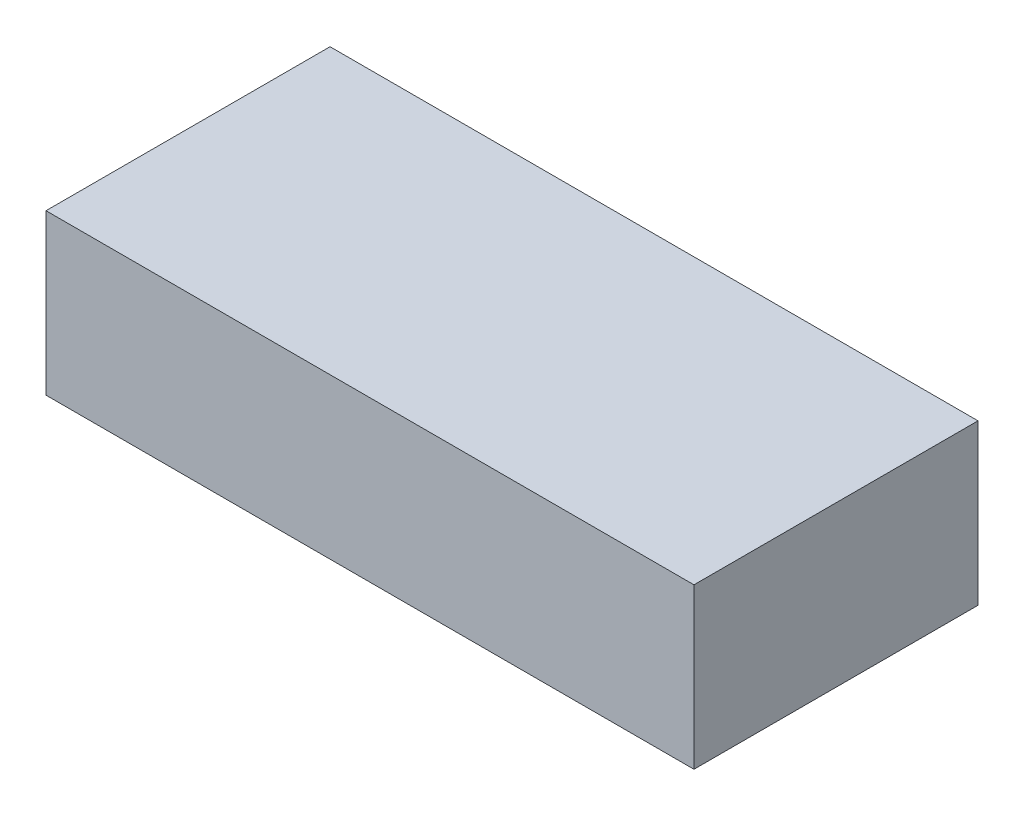
SolidWorks part; units mm, degrees
ref_plane "Front Plane" through (0, 0, 0) normal (0, 0, 1) x (1, 0, 0)
ref_plane "Top Plane" through (0, 0, 0) normal (0, 1, 0) x (1, 0, 0)
ref_plane "Right Plane" through (0, 0, 0) normal (1, 0, 0) x (0, 0, -1)
sketch "Sketch1" plane through (0, 0, 0) normal (0, 1, 0) x (1, 0, 0)
  line L1 (-36.5, 16) -> (36.5, 16)
  line L2 (-36.5, 16) -> (-36.5, -16)
  line L3 (-36.5, -16) -> (36.5, -16)
  line L4 (36.5, 16) -> (36.5, -16)
  line L5 (-36.5, 16) -> (36.5, -16) construction
  line L6 (-36.5, -16) -> (36.5, 16) construction
  point P0 (0, 0)
  dimension "D1" = 32
  dimension "D2" = 73
extrude "Boss-Extrude1" add sketch "Sketch1" along normal blind 18
